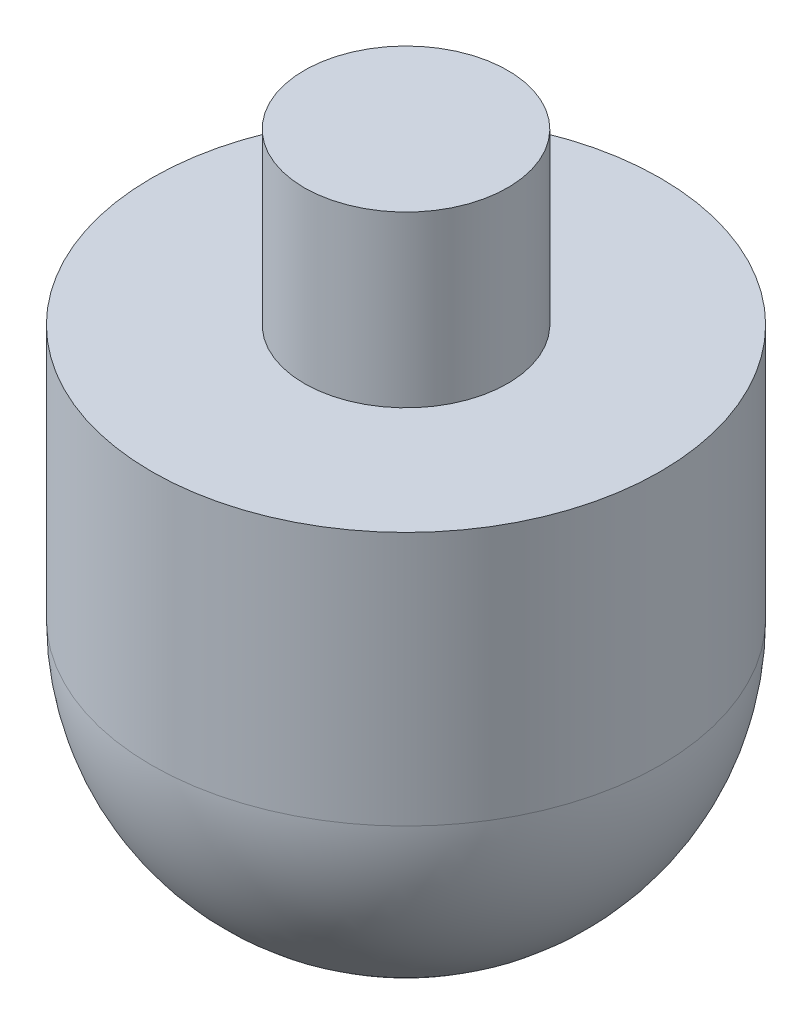
SolidWorks part; units mm, degrees
ref_plane "Front" through (0, 0, 0) normal (0, 0, 1) x (1, 0, 0)
ref_plane "Top" through (0, 0, 0) normal (0, 1, 0) x (1, 0, 0)
ref_plane "Right" through (0, 0, 0) normal (1, 0, 0) x (0, 0, -1)
sketch "Sketch1" plane through (0, 0, 0) normal (0, 0, 1) x (1, 0, 0)
  line L0 (0, 45.6634) -> (0, -88.5473) construction
  line L1 (0, 0) -> (-6, 0)
  line L2 (-6, 0) -> (-6, -10)
  line L3 (-6, -10) -> (-15, -10)
  line L4 (-15, -10) -> (-15, -25)
  line L5 (0, 0) -> (0, -40)
  arc A0 (-15, -25) -> (0, -40) centre (0, -25) ccw
  point P10 (0, 0)
  point P11 (0, 0)
  dimension "D1" = 10
  dimension "D2" = 25
  dimension "D3" = 15
  dimension "D4" = 6
revolve "Revolve1" add sketch "Sketch1" angle 360 about L0
